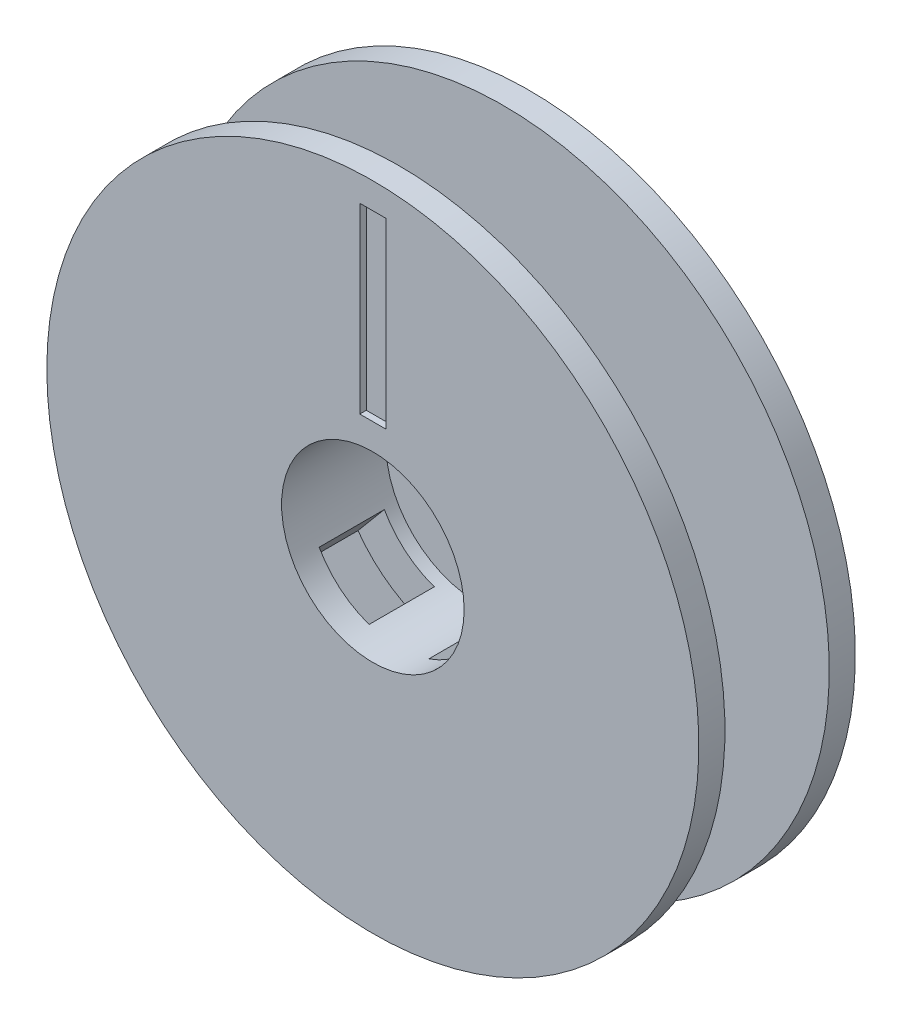
SolidWorks part; units mm, degrees
ref_plane "正面(Front)" through (0, 0, 0) normal (0, 0, 1) x (1, 0, 0)
ref_plane "平面(Top)" through (0, 0, 0) normal (0, 1, 0) x (1, 0, 0)
ref_plane "右側面(Right)" through (0, 0, 0) normal (1, 0, 0) x (0, 0, -1)
sketch "ｽｹｯﾁ1" plane through (0, 0, 0) normal (0, 0, 1) x (1, 0, 0)
  line L0 (0, 0) -> (0, 32.0386) construction
  line L1 (3.75, 6.4952) -> (2.7738, 13.5821)
  line L2 (0, 0) -> (3.75, 6.4952) construction
  arc A0 (2.7738, 13.5821) -> (0, 16) centre (0, 13.2) ccw
  dimension "D1" = 2.8
  dimension "D2" = 7.5
  dimension "D3" = 30
  dimension "D4" = 16
sketch "ｽｹｯﾁ2" plane through (0, 0, 0) normal (0, 0, 1) x (1, 0, 0)
  line L0 (3.75, 6.4952) -> (2.7738, 13.5821) construction
  line L1 (3.75, 6.4952) -> (2.7738, 13.5821)
  line L3 (0, 0) -> (0, 32.0386) construction
  line L4 (0, 0) -> (0, 32.0386) construction
  line L5 (-3.75, 6.4952) -> (-2.7738, 13.5821)
  line L6 (7.5, 0) -> (13.1493, 4.3889)
  line L7 (3.75, 6.4952) -> (10.3755, 9.1932)
  line L8 (3.75, -6.4952) -> (10.3755, -9.1932)
  line L9 (7.5, 0) -> (13.1493, -4.3889)
  line L10 (-3.75, -6.4952) -> (-2.7738, -13.5821)
  line L11 (3.75, -6.4952) -> (2.7738, -13.5821)
  line L12 (-7.5, 0) -> (-13.1493, -4.3889)
  line L13 (-3.75, -6.4952) -> (-10.3755, -9.1932)
  line L14 (-3.75, 6.4952) -> (-10.3755, 9.1932)
  line L15 (-7.5, 0) -> (-13.1493, 4.3889)
  line L16 (0, 0) -> (3.75, 6.4952) construction
  arc A0 (2.7738, 13.5821) -> (0, 16) centre (0, 13.2) ccw construction
  arc A1 (2.7738, 13.5821) -> (-2.7738, 13.5821) centre (0, 13.2) ccw
  arc A2 (13.1493, 4.3889) -> (10.3755, 9.1932) centre (11.4315, 6.6) ccw
  arc A3 (10.3755, -9.1932) -> (13.1493, -4.3889) centre (11.4315, -6.6) ccw
  arc A4 (-2.7738, -13.5821) -> (2.7738, -13.5821) centre (0, -13.2) ccw
  arc A5 (-13.1493, -4.3889) -> (-10.3755, -9.1932) centre (-11.4315, -6.6) ccw
  arc A6 (-10.3755, 9.1932) -> (-13.1493, 4.3889) centre (-11.4315, 6.6) ccw
  dimension "D2" = 7.5
  dimension "D3" = 30
  dimension "D1" = 6
sketch "ｽｹｯﾁ3" plane through (0, 0, 0) normal (0, 0, 1) x (1, 0, 0)
  circle A0 centre (0, 0) radius 13
  dimension "D1" = 26
extrude "ﾎﾞｽ - 押し出し1" add sketch "ｽｹｯﾁ3" along normal blind 5
extrude "ｶｯﾄ - 押し出し2" cut sketch "ｽｹｯﾁ2" along normal blind 2.5
sketch "ｽｹｯﾁ4" plane through (0, 0, 5) normal (0, 0, 1) x (1, 0, 0)
  circle A0 centre (0, 0) radius 10
  dimension "D1" = 20
sketch "ｽｹｯﾁ5" plane through (0, 0, 0) normal (0, 1, 0) x (1, 0, 0)
  line L0 (0, 0) -> (0, -21.9976) construction
  line L1 (0, -5) -> (25, -5)
  line L3 (25, -5) -> (25, -7)
  line L4 (25, -7) -> (10, -7)
  line L5 (10, -7) -> (10, -15)
  line L6 (10, -15) -> (25, -15)
  line L7 (25, -15) -> (25, -17)
  line L8 (25, -17) -> (0, -17)
  line L9 (0, -5) -> (0, -17)
  line L10 (-10, -5) -> (10, -5) construction
  dimension "D1" = 2
  dimension "D2" = 2
  dimension "D3" = 8
  dimension "D4" = 10
  dimension "D5" = 25
revolve "回転1" add sketch "ｽｹｯﾁ5" angle 360 about L0
sketch "ｽｹｯﾁ6" plane through (0, 0, 17) normal (0, 0, 1) x (1, 0, 0)
  circle A0 centre (0, 0) radius 2
  dimension "D1" = 4
extrude "ｶｯﾄ - 押し出し3" cut sketch "ｽｹｯﾁ6" against normal through all
sketch "ｽｹｯﾁ7" plane through (0, 0, 17) normal (0, 0, 1) x (1, 0, 0)
  circle A0 centre (0, 0) radius 7
  dimension "D1" = 14
extrude "ｶｯﾄ - 押し出し4" cut sketch "ｽｹｯﾁ7" against normal blind 8
sketch "ｽｹｯﾁ8" plane through (0, 0, 17) normal (0, 0, 1) x (1, 0, 0)
  line L0 (14.7902, 2.5) -> (9.6825, 2.5)
  line L1 (12.9904, 7.5) -> (6.6144, 7.5)
  line L2 (0, 0) -> (27.9307, 0) construction
  line L3 (14.7902, -2.5) -> (9.6825, -2.5)
  line L4 (12.9904, -7.5) -> (6.6144, -7.5)
  circle A0 centre (0, 0) radius 10 construction
  arc A1 (14.7902, 2.5) -> (12.9904, 7.5) centre (0, 0) ccw
  arc A2 (9.6825, 2.5) -> (6.6144, 7.5) centre (0, 0) ccw
  arc A3 (9.6825, -2.5) -> (6.6144, -7.5) centre (0, 0) cw
  arc A4 (14.7902, -2.5) -> (12.9904, -7.5) centre (0, 0) cw
  dimension "D1" = 20
  dimension "D4" = 5
  dimension "D2" = 5
  dimension "D3" = 5
extrude "ｶｯﾄ - 押し出し5" [suppressed] cut sketch "ｽｹｯﾁ8" against normal up to next contours A4 L3 A3 L4 | A2 L0 A1 L1
sketch "ｽｹｯﾁ9" plane through (0, 0, 15) normal (0, 0, -1) x (-1, 0, 0)
  line L0 (0, 0) -> (-20.5505, -24.4911) construction
  line L1 (0, 0) -> (0, -32.4809) construction
  line L2 (-3.8435, -0.6912) -> (-11.5569, -9.8837)
  line L3 (-3.8435, -0.6912) -> (-0.0133, -3.9051)
  line L4 (-11.5569, -9.8837) -> (-7.7267, -13.0976)
  line L5 (-0.0133, -3.9051) -> (-7.7267, -13.0976)
  line L6 (-3.8435, -0.6912) -> (-7.7267, -13.0976) construction
  line L7 (-11.5569, -9.8837) -> (-0.0133, -3.9051) construction
  point P5 (-5.7851, -6.8944)
  dimension "D1" = 40
  dimension "D2" = 5
  dimension "D3" = 12
  dimension "D4" = 3
extrude "ｶｯﾄ - 押し出し6" cut sketch "ｽｹｯﾁ9" along normal blind 5
mirror "ﾐﾗｰ1" about plane through (0, 0, 0) normal (1, 0, 0) of "ｶｯﾄ - 押し出し6"
fillet "ﾌｨﾚｯﾄ1" radius 1 2 edges at (4.3087, -9.0242, 12.5) (-4.3087, -9.0242, 12.5)
sketch "ｽｹｯﾁ10" plane through (0, 0, 17) normal (0, 0, 1) x (1, 0, 0)
  line L0 (0, 0) -> (0, 32.0386) construction
  line L1 (-1, 23) -> (1, 23)
  line L2 (-1, 23) -> (-1, 9)
  line L3 (-1, 9) -> (1, 9)
  line L4 (1, 23) -> (1, 9)
  line L5 (-1, 23) -> (1, 9) construction
  line L6 (-1, 9) -> (1, 23) construction
  circle A0 centre (0, 0) radius 25 construction
  circle A2 centre (0, 0) radius 7 construction
  point P0 (0, 16)
  dimension "D1" = 2
  dimension "D2" = 2
  dimension "D3" = 2
extrude "ｶｯﾄ - 押し出し7" cut sketch "ｽｹｯﾁ10" against normal blind 0.5
